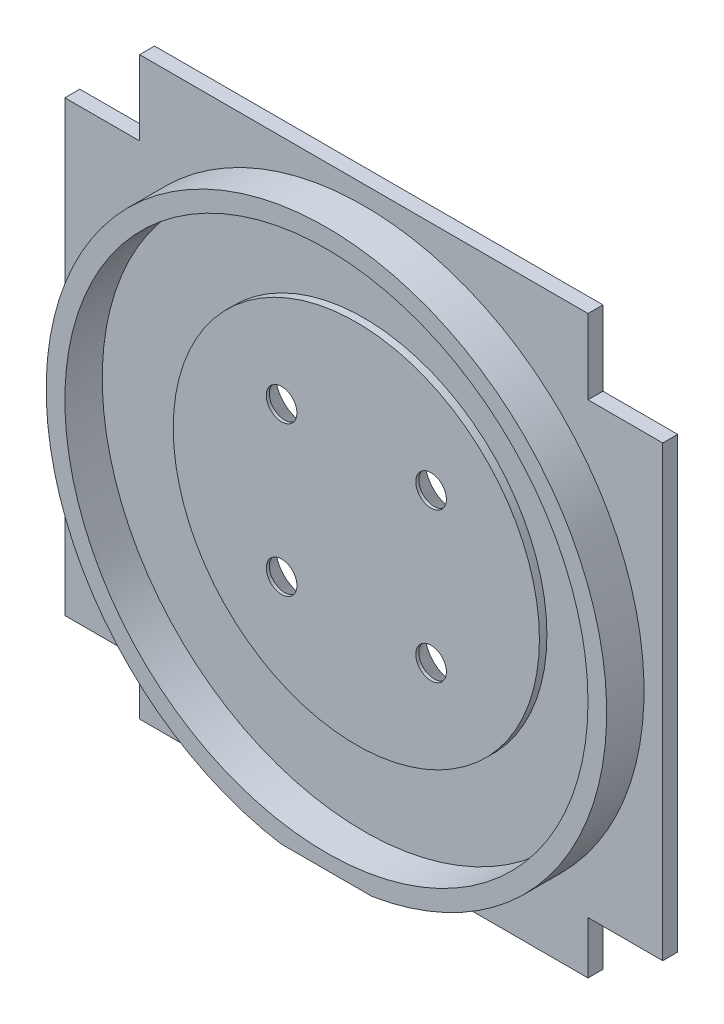
SolidWorks part; units mm, degrees
ref_plane "Plan de face" through (0, 0, 0) normal (0, 0, 1) x (1, 0, 0)
ref_plane "Plan de dessus" through (0, 0, 0) normal (0, 1, 0) x (1, 0, 0)
ref_plane "Plan de droite" through (0, 0, 0) normal (1, 0, 0) x (0, 0, -1)
sketch "Esquisse1" plane through (0, 0, 0) normal (0, 0, 1) x (1, 0, 0)
  line L1 (0, 0) -> (80, 0)
  line L2 (0, 0) -> (0, 80)
  line L3 (0, 80) -> (80, 80)
  line L4 (80, 0) -> (80, 80)
  dimension "D1" = 80
  dimension "D2" = 80
extrude "Boss.-Extru.1" add sketch "Esquisse1" along normal blind 2
sketch "Esquisse2" plane through (0, 0, 2) normal (0, 0, 1) x (1, 0, 0)
  line L0 (0, 80) -> (0, 0) construction
  line L1 (0, 0) -> (80, 0) construction
  circle A0 centre (40, 40) radius 24.5
  dimension "D1" = 49
  dimension "D2" = 40
  dimension "D3" = 40
extrude "Boss.-Extru.2" add sketch "Esquisse2" along normal blind 1
sketch "Esquisse3" plane through (0, 0, 0) normal (0, 0, -1) x (-1, 0, 0)
  line L0 (-80, 0) -> (-80, 80) construction
  line L1 (0, 80) -> (0, 0) construction
  line L2 (-80, 80) -> (0, 80) construction
  line L3 (0, 0) -> (-80, 0) construction
  circle A0 centre (-50, 50) radius 2.05
  circle A1 centre (-50, 30) radius 2.05
  circle A2 centre (-30, 30) radius 2.05
  circle A3 centre (-30, 50) radius 2.05
  dimension "D1" = 4.1
  dimension "D2" = 4.1
  dimension "D3" = 4.1
  dimension "D4" = 4.1
  dimension "D5" = 30
  dimension "D6" = 30
  dimension "D7" = 30
  dimension "D8" = 30
  dimension "D9" = 30
  dimension "D10" = 30
  dimension "D11" = 30
  dimension "D12" = 30
extrude "Enlèv. mat.-Extru.1" cut sketch "Esquisse3" against normal through all
chamfer "Chanfrein1" distance 1.75 angle 56 4 edges at (47.95, 30, 0) (27.95, 30, 0) (27.95, 50, 0) (47.95, 50, 0)
sketch "Esquisse4" plane through (0, 0, 2) normal (0, 0, 1) x (1, 0, 0)
  line L0 (80, 0) -> (80, 80) construction
  line L1 (80, 80) -> (0, 80) construction
  circle A0 centre (40, 40) radius 35
  circle A1 centre (40, 40) radius 37.5
  dimension "D3" = 75
  dimension "D4" = 70
  dimension "D1" = 40
  dimension "D2" = 40
extrude "Boss.-Extru.3" add sketch "Esquisse4" along normal blind 5
sketch "Esquisse5" plane through (0, 0, 0) normal (0, 0, -1) x (-1, 0, 0)
  line L0 (0, 80) -> (0, 0) construction
  line L1 (-80, 0) -> (0, 0)
  line L2 (-80, 0) -> (-80, 3)
  line L3 (-80, 3) -> (0, 3)
  line L4 (0, 0) -> (0, 3)
  dimension "D1" = 3
extrude "Enlèv. mat.-Extru.2" cut sketch "Esquisse5" against normal through all
sketch "Esquisse6" plane through (0, 0, 0) normal (0, 0, -1) x (-1, 0, 0)
  line L1 (-80, 80) -> (-70, 80)
  line L2 (-80, 80) -> (-80, 70)
  line L3 (-80, 70) -> (-70, 70)
  line L4 (-70, 80) -> (-70, 70)
  line L5 (0, 80) -> (-10, 80)
  line L6 (0, 80) -> (0, 70)
  line L7 (0, 70) -> (-10, 70)
  line L8 (-10, 80) -> (-10, 70)
  line L9 (0, 3) -> (-10, 3)
  line L10 (0, 3) -> (0, 10)
  line L11 (0, 10) -> (-10, 10)
  line L12 (-10, 3) -> (-10, 10)
  line L13 (-80, 3) -> (-70, 3)
  line L14 (-80, 3) -> (-80, 10)
  line L15 (-80, 10) -> (-70, 10)
  line L16 (-70, 3) -> (-70, 10)
  dimension "D1" = 10
  dimension "D2" = 10
  dimension "D3" = 10
  dimension "D4" = 10
  dimension "D5" = 10
  dimension "D6" = 7
  dimension "D7" = 7
  dimension "D8" = 10
extrude "Enlèv. mat.-Extru.3" cut sketch "Esquisse6" against normal through all
